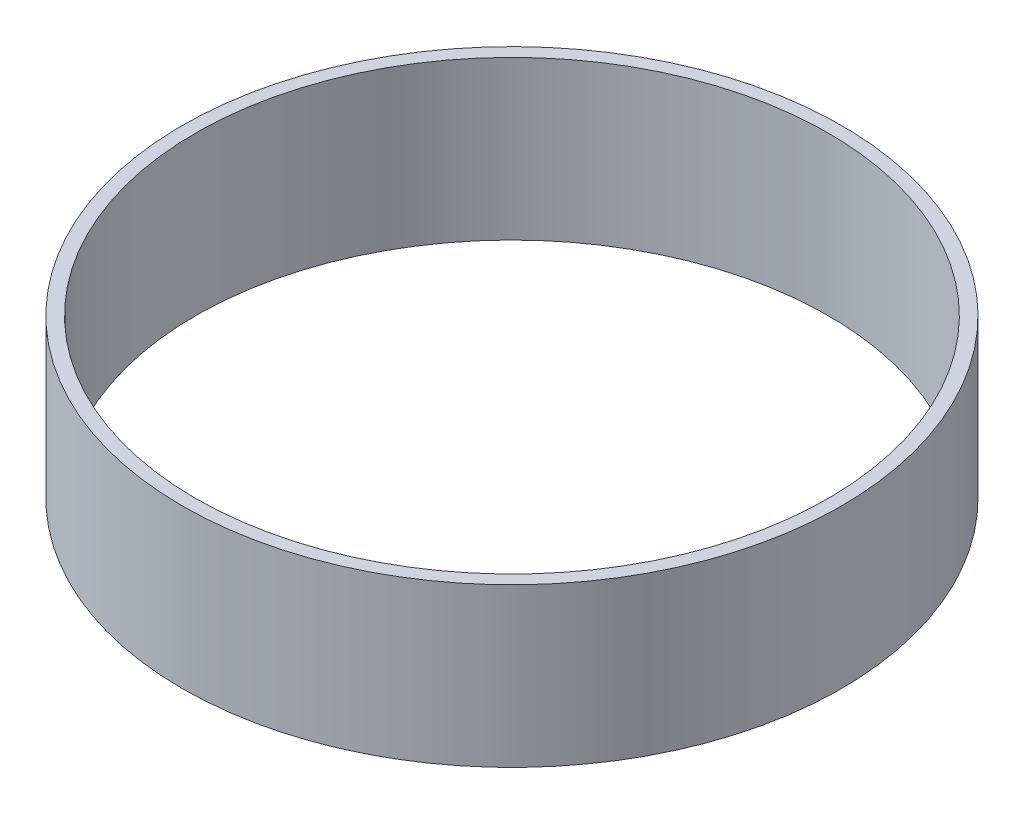
SolidWorks part; units mm, degrees
material "AISI 316 Stainless Steel Sheet (SS)"
ref_plane "Front Plane" through (0, 0, 0) normal (0, 0, 1) x (1, 0, 0)
ref_plane "Top Plane" through (0, 0, 0) normal (0, 1, 0) x (1, 0, 0)
ref_plane "Right Plane" through (0, 0, 0) normal (1, 0, 0) x (0, 0, -1)
sketch "Sketch1" plane through (0, 0, 0) normal (0, 1, 0) x (1, 0, 0)
  circle A0 centre (0, 0) radius 152.4
  circle A1 centre (0, 0) radius 158.75
  dimension "D1" = 317.5
  dimension "D2" = 6.35
extrude "Boss-Extrude1" add sketch "Sketch1" against normal blind 76.2
